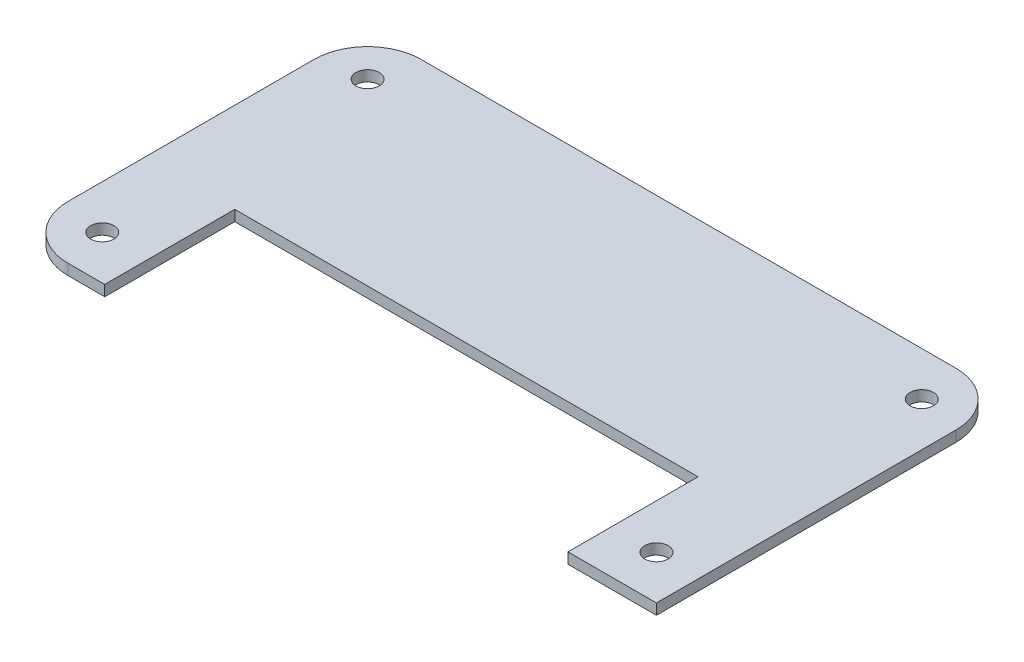
SolidWorks part; units mm, degrees
ref_plane "Alzado" through (0, 0, 0) normal (0, 0, 1) x (1, 0, 0)
ref_plane "Planta" through (0, 0, 0) normal (0, 1, 0) x (1, 0, 0)
ref_plane "Vista lateral" through (0, 0, 0) normal (1, 0, 0) x (0, 0, -1)
sketch "Croquis1" plane through (0, 0, 0) normal (0, 1, 0) x (1, 0, 0)
  line L0 (0, 0) -> (0, 56)
  line L1 (-10, 66) -> (-110, 66)
  line L2 (-120, 56) -> (-120, 10)
  line L3 (-110, 0) -> (-103.1384, 0)
  line L4 (-16.5419, 0) -> (0, 0)
  line L12 (-103.1384, 0) -> (-103.1384, 24.3157)
  line L13 (-103.1384, 24.3157) -> (-16.5419, 24.3157)
  line L14 (-16.5419, 0) -> (-16.5419, 24.3157)
  arc A0 (0, 56) -> (-10, 66) centre (-10, 56) ccw
  arc A1 (-110, 66) -> (-120, 56) centre (-110, 56) ccw
  arc A2 (-120, 10) -> (-110, 0) centre (-110, 10) ccw
  circle A3 centre (-8.2, 8.2) radius 2.175
  circle A4 centre (-8.2, 57.8) radius 2.175
  circle A5 centre (-111.8, 57.8) radius 2.175
  circle A6 centre (-111.8, 8.2) radius 2.175
extrude "Saliente-Extruir1" add sketch "Croquis1" along normal blind 2
